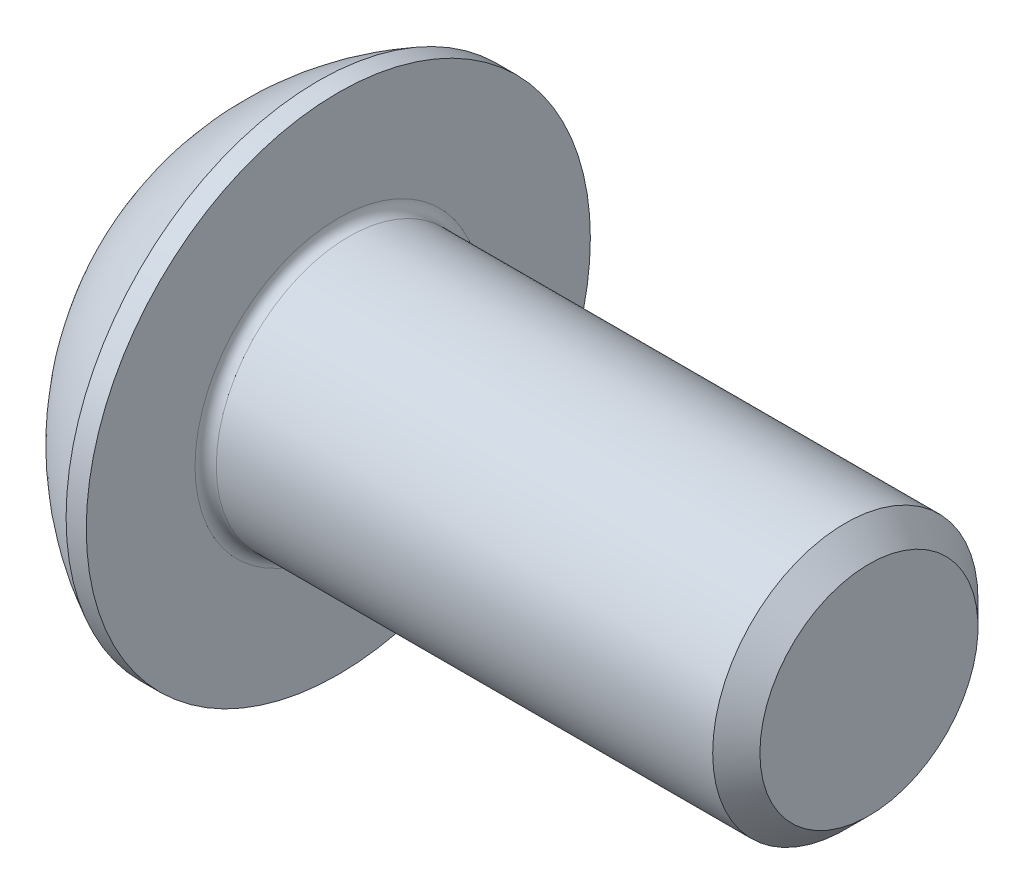
SolidWorks part; units mm, degrees
ref_plane "Plane1" through (0, 0, 0) normal (0, 0, 1) x (1, 0, 0)
ref_plane "Plane2" through (0, 0, 0) normal (0, 1, 0) x (1, 0, 0)
ref_plane "Plane3" through (0, 0, 0) normal (1, 0, 0) x (0, 0, -1)
sketch "BodySke" plane through (0, 0, 0) normal (0, 0, 1) x (1, 0, 0)
  line L0 (12.75, 0) -> (12.75, 2.055)
  line L1 (12.305, 2.5) -> (2.75, 2.5)
  line L2 (2.75, 2.5) -> (2.75, 4.75)
  line L3 (2.75, 4.75) -> (2.37, 4.75)
  line L4 (0, 0) -> (101.6, 0) construction
  line L5 (2.75, -4.75) -> (2.37, -4.75) construction
  line L6 (55.6768, -2.5) -> (2.75, -2.5) construction
  line L7 (12.75, 0) -> (0, 0)
  line L8 (0, 2.375) -> (0, -2.375) construction
  line L9 (0, 0) -> (0, 2.375)
  line L10 (12.75, 2.055) -> (12.305, 2.5)
  line L11 (12.75, -2.055) -> (12.305, -2.5) construction
  line L12 (3.55, 9.525) -> (3.55, -2.5) construction
  line L13 (2.75, 9.525) -> (2.75, -2.5) construction
  arc A1 (0, 2.375) -> (2.37, 4.75) centre (4.755, 0) cw
  dimension "Diameter" = 5
  dimension "Length" = 10
  dimension "Head_dia" = 9.5
  dimension "D1" = 4.75
  dimension "Head_ht" = 2.75
  dimension "Head_side_ht" = 0.38
  dimension "Minor_dia" = 4.11
  dimension "Body_ch_ang" = 45
  dimension "Advance" = 0.8
  dimension "Thread_nom" = 10
revolve "BaseBody" add sketch "BodySke" angle 360 about L4
cosmetic thread "ThreadCosmetic" [suppressed] parameters "Thread_length"=8.4, "Thread_minor"=4.11
fillet "Fillet1" radius 0.2 1 edges at (2.75, 0, 2.5)
sketch "Sketch2" plane through (0, 0, 0) normal (0, 0, 1) x (1, 0, 0)
  line L0 (0, 1.5) -> (1.56, 1.5)
  line L1 (1.56, 1.5) -> (2.426, 0)
  line L3 (2.426, 0) -> (0, 0)
  line L4 (0, 0) -> (0, 1.5)
  line L5 (0, -1.5) -> (1.56, -1.5) construction
  line L6 (0, 0) -> (47.625, 0) construction
  dimension "D2" = 60
  dimension "PreBroach_depth" = 1.56
  dimension "PreBroach_dia" = 3
revolve "PreBroach" cut sketch "Sketch2" angle 360 about L6
sketch "Sketch3" plane through (0, 0, 0) normal (1, 0, 0) x (0, 0, -1)
  line L0 (-1.5, -0.866) -> (-1.5, 0.866)
  line L1 (-1.5, 0.866) -> (0, 1.7321)
  line L2 (0, 1.7321) -> (1.5, 0.866)
  line L3 (1.5, 0.866) -> (1.5, -0.866)
  line L4 (1.5, -0.866) -> (0, -1.7321)
  line L5 (0, -1.7321) -> (-1.5, -0.866)
  dimension "Hex_size" = 3
  dimension "D3" = 3
  dimension "D1" = 1.5
  dimension "D2" = 1.5
extrude "Hex" cut sketch "Sketch3" along normal blind 1.56
sketch "ThdSchSke" plane through (0, 0, 0) normal (0, 0, 1) x (1, 0, 0)
  line L0 (4.35, -2.055) -> (4.0384, -2.5)
  line L1 (4.35, -2.055) -> (4.6616, -2.5)
  line L2 (4.6616, -2.5) -> (4.6616, -3.125)
  line L3 (-3.175, 0) -> (5.1513, 0) construction
  line L5 (4.6616, -3.125) -> (4.0384, -3.125)
  line L6 (4.0384, -3.125) -> (4.0384, -2.5)
  dimension "Diameter" = 5
  dimension "Thread_minor" = 4.11
  dimension "SideAngle" = 55
  dimension "VeeAngle" = 70
  dimension "Overcut" = 6.25
  dimension "Start" = 4.35
revolve "ThreadSchematic" [suppressed] cut sketch "ThdSchSke" angle 360 about L3
pattern_linear "ThdSchPat" [suppressed]
equation "\"D1@BodySke\" = \"Head_dia@BodySke\" * .5"
equation "\"Thread_minor@ThreadCosmetic\" = \"Minor_dia@BodySke\""
equation "\"D1@Sketch3\" = \"Hex_size@Sketch3\" / 2"
equation "\"D2@Sketch3\" = \"D1@Sketch3\""
equation "\"D3@Sketch3\" = \"Hex_size@Sketch3\""
equation "\"Thread_length@ThreadCosmetic\" = ((sgn( (\"Length@BodySke\" - \"Advance@BodySke\" * 2.0) - \"Thread_nom@BodySke\" )-1)*( (\"Length@BodySke\" - \"Advance@BodySke\" * 2.0) - \"Thread_nom@BodySke\" ))/-2+ \"Thread_nom@BodySke\""
equation "\"Thread_minor@ThdSchSke\" = \"Minor_dia@BodySke\""
equation "\"Diameter@ThdSchSke\" = \"Diameter@BodySke\""
equation "\"Overcut@ThdSchSke\" = \"Diameter@BodySke\" * 1.25"
equation "\"Start@ThdSchSke\" = \"Head_ht@BodySke\" + \"Length@BodySke\" - \"Thread_length@ThreadCosmetic\"  '---Non-countersunk---"
equation "\"Num_threads@ThdSchPat\" = int( \"Thread_length@ThreadCosmetic\" / \"Advance@BodySke\" + 0.999 )  + 1"
equation "\"Advance@ThdSchPat\" = \"Thread_length@ThreadCosmetic\" /  (\"Num_threads@ThdSchPat\" - 1) 'relax it"
equation "\"Num_threads@ThdSchPat\" = \"Num_threads@ThdSchPat\" - sgn( \"Num_threads@ThdSchPat\" - 1) '---chamfered tips only---"
